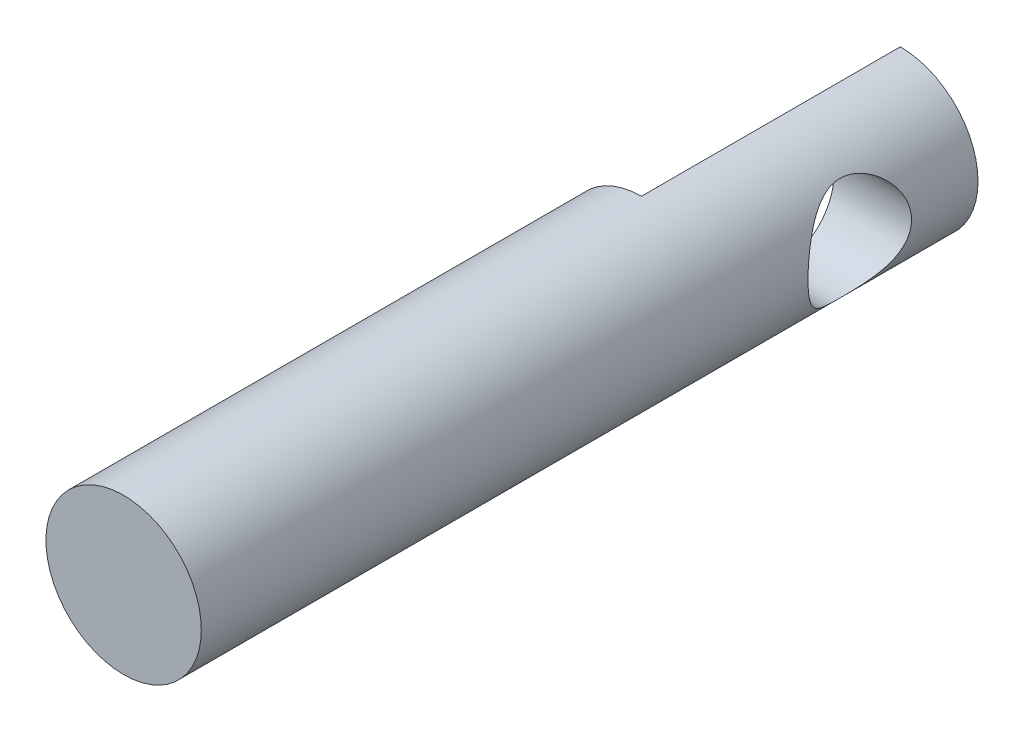
SolidWorks part; units mm, degrees
ref_plane "Front Plane" through (0, 0, 0) normal (0, 0, 1) x (1, 0, 0)
ref_plane "Top Plane" through (0, 0, 0) normal (0, 1, 0) x (1, 0, 0)
ref_plane "Right Plane" through (0, 0, 0) normal (1, 0, 0) x (0, 0, -1)
sketch "Sketch1" plane through (0, 0, 0) normal (0, 0, 1) x (1, 0, 0)
  circle A0 centre (0, 0) radius 1.5
  dimension "D1" = 3
extrude "Boss-Extrude1" add sketch "Sketch1" along normal blind 15
sketch "Sketch2" plane through (0, 0, 0) normal (1, 0, 0) x (0, 0, -1)
  line L0 (0, -1.5) -> (0, 1.5) construction
  line L1 (-5, 2.3064) -> (0, 2.3064)
  line L2 (-5, 2.3064) -> (-5, -2.3906)
  line L3 (-5, -2.3906) -> (0, -2.3906)
  line L4 (0, 2.3064) -> (0, -2.3906)
  dimension "D1" = 5
extrude "Cut-Extrude1" cut sketch "Sketch2" against normal blind 30
sketch "Sketch3" plane through (0, 0, 0) normal (-1, 0, 0) x (0, 0, 1)
  circle A0 centre (2.2825, 0) radius 1
  dimension "D1" = 2
extrude "Cut-Extrude2" cut sketch "Sketch3" against normal blind 30
